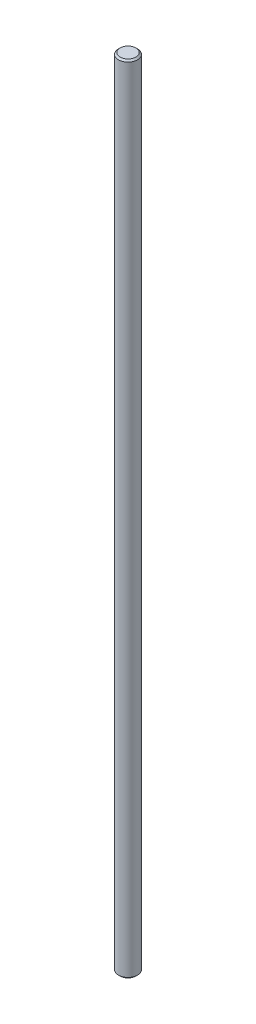
SolidWorks part; units mm, degrees
ref_plane "Front Plane" through (0, 0, 0) normal (0, 0, 1) x (1, 0, 0)
ref_plane "Top Plane" through (0, 0, 0) normal (0, 1, 0) x (1, 0, 0)
ref_plane "Right Plane" through (0, 0, 0) normal (1, 0, 0) x (0, 0, -1)
sketch "Sketch1" plane through (0, 0, 0) normal (0, 1, 0) x (1, 0, 0)
  circle A0 centre (0, 0) radius 3
  dimension "D1" = 6
extrude "Boss-Extrude1" add sketch "Sketch1" along normal blind 250
chamfer "Chamfer1" distance 0.5 2 edges at (0, 250, 3) (0, 0, 3)
